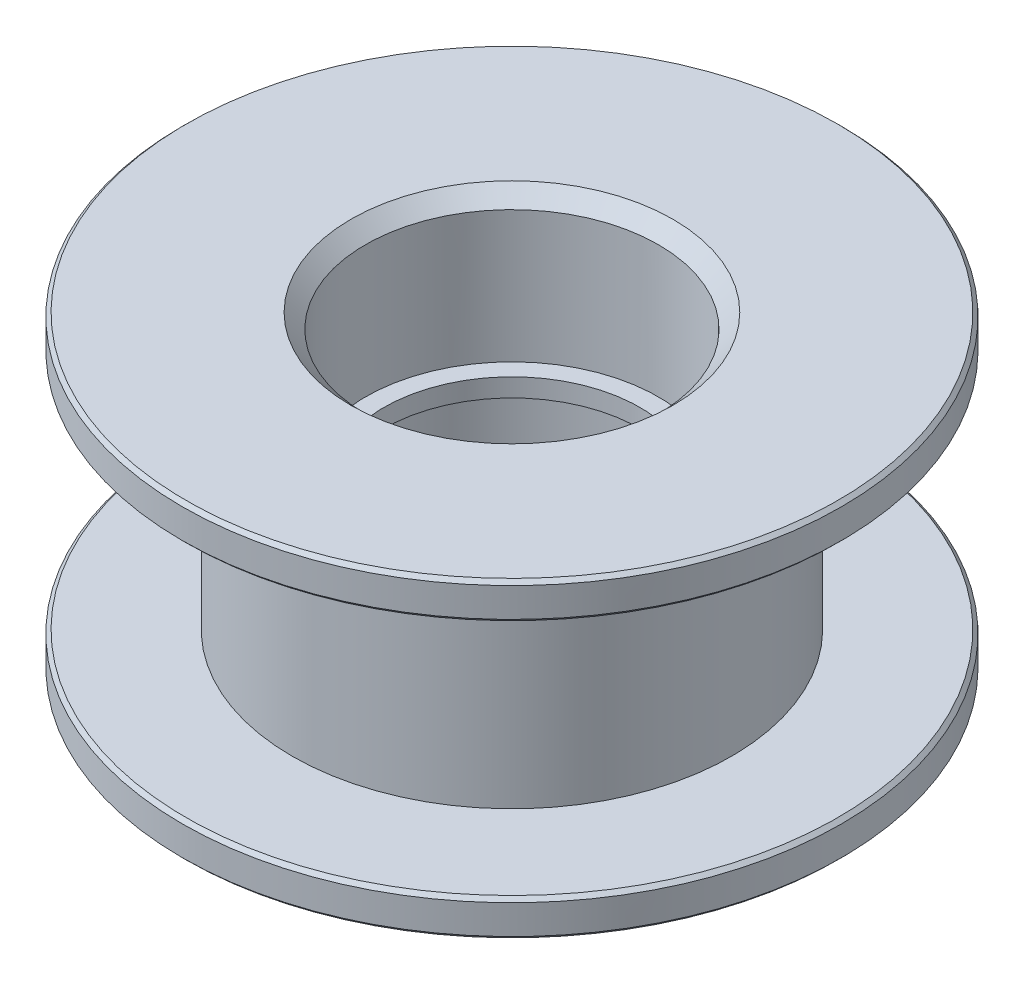
SolidWorks part; units mm, degrees
material "6061 Alloy"
ref_plane "Front Plane" through (0, 0, 0) normal (0, 0, 1) x (1, 0, 0)
ref_plane "Top Plane" through (0, 0, 0) normal (0, 1, 0) x (1, 0, 0)
ref_plane "Right Plane" through (0, 0, 0) normal (1, 0, 0) x (0, 0, -1)
sketch "BodyS" plane through (0, 0, 0) normal (0, 0, 1) x (1, 0, 0)
  line L0 (6, -3.25) -> (6, 3.25)
  line L1 (6, 3.25) -> (9, 3.25)
  line L2 (9, 3.25) -> (9, 4.25)
  line L3 (9, 4.25) -> (4, 4.25)
  line L4 (4, 4.25) -> (4, 0.25)
  line L5 (4, 0.25) -> (3.5, 0.25)
  line L6 (3.5, 0.25) -> (3.5, -0.25)
  line L7 (3.5, -0.25) -> (4, -0.25)
  line L8 (4, -0.25) -> (4, -4.25)
  line L9 (4, -4.25) -> (9, -4.25)
  line L10 (9, -4.25) -> (9, -3.25)
  line L11 (9, -3.25) -> (6, -3.25)
  line L12 (0, 0) -> (3.5, 0) construction
  line L13 (0, 4.25) -> (0, -4.25) construction
  dimension "BearingOD" = 8
  dimension "Height" = 8.5
  dimension "FlangeHeight" = 1
  dimension "BearingHeight" = 4
  dimension "BearingRestDiaControl" = 0.5
  dimension "RefBodyInnerDiameter" = 7
  dimension "FlangeDiaControl" = 5
  dimension "RefFlangeDia" = 18
  dimension "BeltPathDiaControl" = 2
  dimension "RefBeltPathDia" = 12
revolve "Body" add sketch "BodyS" angle 360 about L13
chamfer "InnerC" distance 0.4 angle 45 2 edges at (0, -4.25, 4) (0, 4.25, 4)
chamfer "OuterC" distance 0.1 angle 45 4 edges at (0, -4.25, 9) (0, -3.25, 9) (0, 3.25, 9) (0, 4.25, 9)
